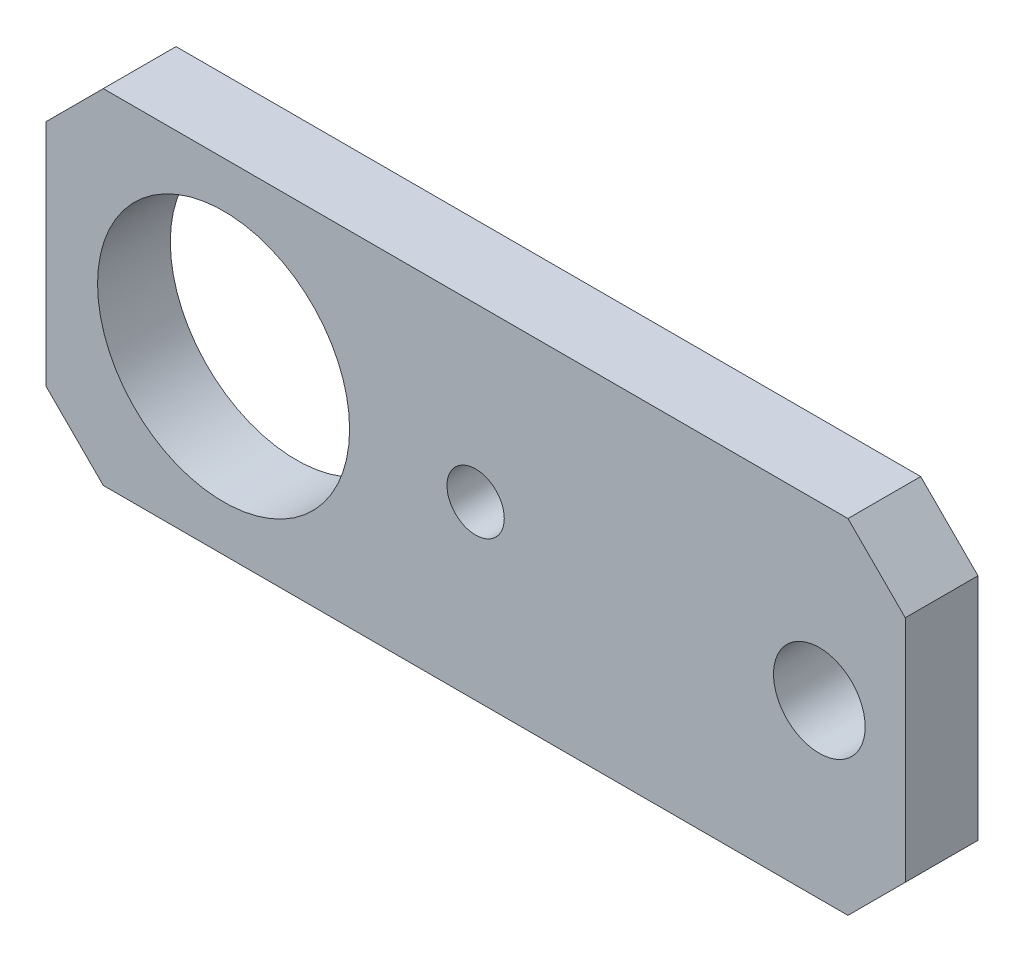
SolidWorks part; units mm, degrees
ref_plane "Front Plane" through (0, 0, 0) normal (0, 0, 1) x (1, 0, 0)
ref_plane "Top Plane" through (0, 0, 0) normal (0, 1, 0) x (1, 0, 0)
ref_plane "Right Plane" through (0, 0, 0) normal (1, 0, 0) x (0, 0, -1)
sketch "Sketch1" plane through (0, 0, 0) normal (0, 0, 1) x (1, 0, 0)
  line L5 (-37.5, 15) -> (37.5, 15)
  line L6 (-37.5, 15) -> (-37.5, -15)
  line L7 (-37.5, -15) -> (37.5, -15)
  line L8 (37.5, 15) -> (37.5, -15)
  circle A0 centre (-22, 0) radius 11
  circle A1 centre (0, 0) radius 2.5
  circle A2 centre (30, 0) radius 4
  point P0 (0, 0)
  point P6 (0, 15)
  point P8 (-37.5, 0)
  point P15 (0, 0)
  dimension "D3" = 22
  dimension "D4" = 8
  dimension "D5" = 5
  dimension "D1" = 30
  dimension "D2" = 75
  dimension "D6" = 30
  dimension "D7" = 22
extrude "Boss-Extrude1" add sketch "Sketch1" along normal blind 6.35
chamfer "Chamfer1" distance 5 angle 45 4 edges at (37.5, -15, 3.175) (37.5, 15, 3.175) (-37.5, -15, 3.175) (-37.5, 15, 3.175)
